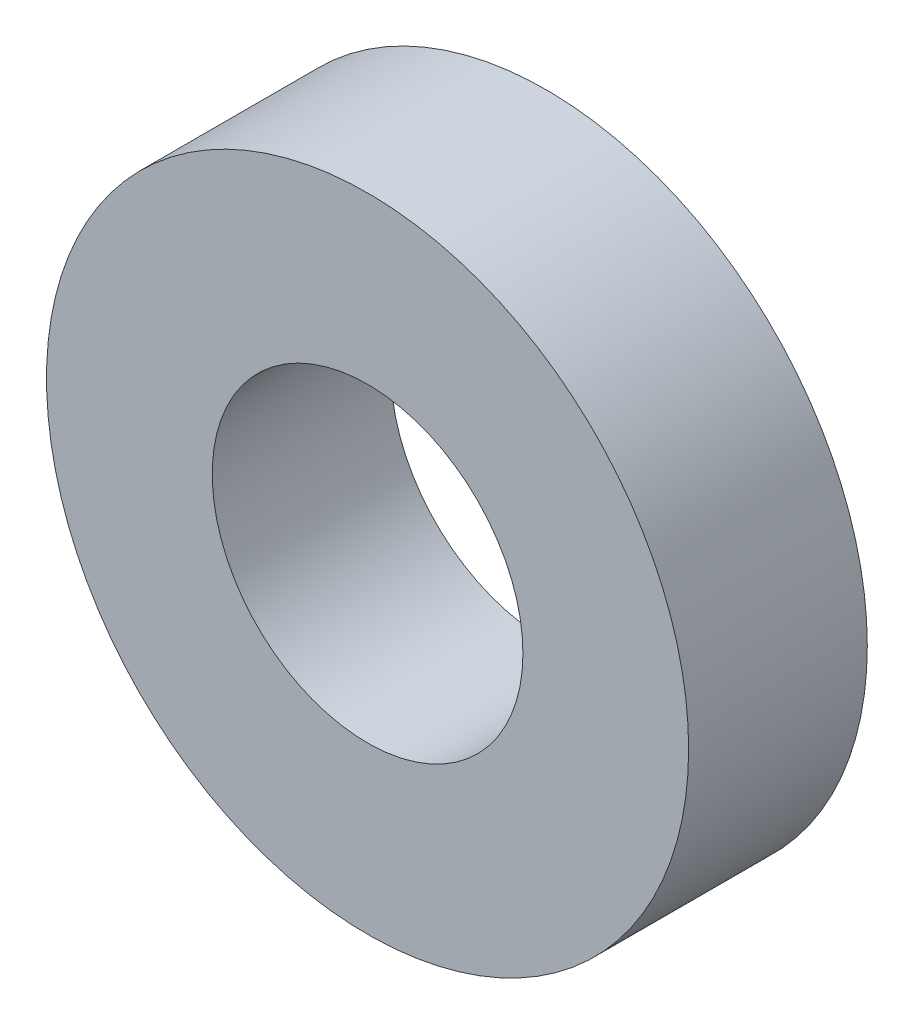
SolidWorks part; units mm, degrees
ref_plane "前视基准面" through (0, 0, 0) normal (0, 0, 1) x (1, 0, 0)
ref_plane "上视基准面" through (0, 0, 0) normal (0, 1, 0) x (1, 0, 0)
ref_plane "右视基准面" through (0, 0, 0) normal (1, 0, 0) x (0, 0, -1)
sketch "草图1" plane through (0, 0, 0) normal (1, 0, 0) x (0, 0, -1)
  line L0 (-27.369, 0) -> (29.6819, 0)
  line L2 (-8.0987, 31) -> (9.1513, 31)
  line L3 (-8.0987, 31) -> (-8.0987, 15)
  line L4 (-8.0987, 15) -> (9.1513, 15)
  line L5 (9.1513, 31) -> (9.1513, 15)
  point P3 (1.9013, 23)
  dimension "D1" = 15
  dimension "D2" = 31
  dimension "D3" = 17.25
revolve "旋转1" add sketch "草图1" angle 360 about L0
